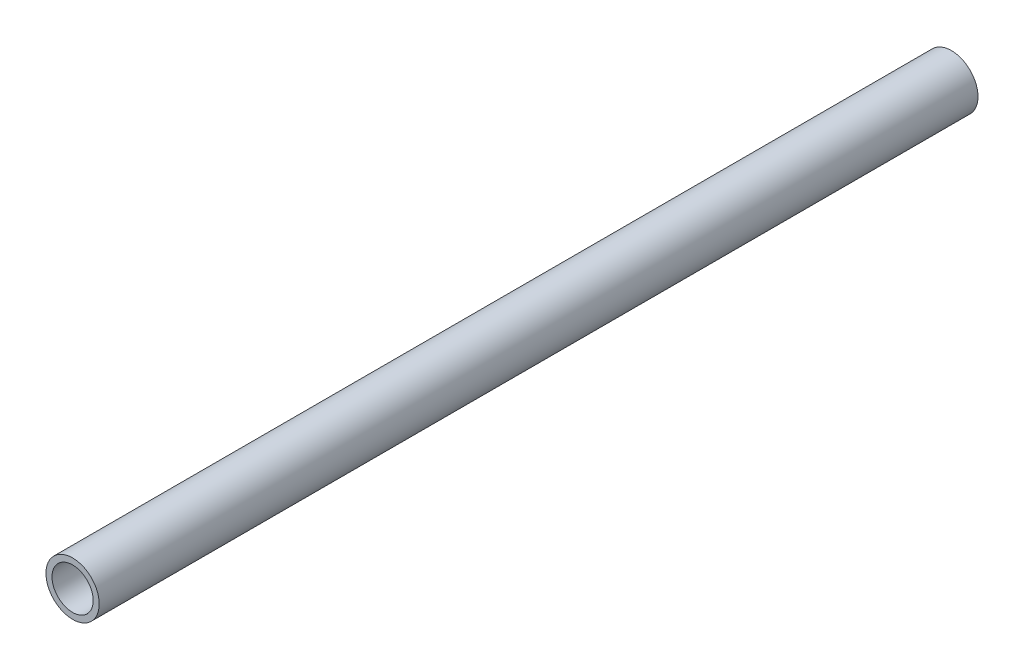
SolidWorks part; units mm, degrees
ref_plane "Front Plane" through (0, 0, 0) normal (0, 0, 1) x (1, 0, 0)
ref_plane "Top Plane" through (0, 0, 0) normal (0, 1, 0) x (1, 0, 0)
ref_plane "Right Plane" through (0, 0, 0) normal (1, 0, 0) x (0, 0, -1)
sketch "Sketch1" plane through (0, 0, 0) normal (0, 0, 1) x (1, 0, 0)
  circle A0 centre (0, 0) radius 6.1595 construction
  circle A1 centre (0, 0) radius 4.7625 construction
  point P4 (4.7625, 0)
  point P5 (6.1595, 0)
  dimension "OD" = 12.319
  dimension "ID" = 9.525
  dimension "Wall Thickness" = 1.397
sketch "Sketch2" plane through (0, 0, 0) normal (1, 0, 0) x (0, 0, -1)
  line L0 (-101.6, 0) -> (101.6, 0) construction
  line L1 (-101.6, -6.1595) -> (-101.6, 6.1595) construction
  line L2 (-101.6, 6.1595) -> (101.6, 6.1595) construction
  line L3 (101.6, -6.1595) -> (101.6, 6.1595) construction
  line L5 (-101.6, -6.1595) -> (101.6, -6.1595) construction
  point P0 (-89.281, 0)
  point P3 (0, 0)
  point P7 (0, 6.1595)
  point P8 (89.281, 0)
  point P11 (-101.6, 0)
  point P13 (101.6, 0)
  dimension "Length" = 203.2
  dimension "D1" = 12.319
  dimension "D2" = 12.319
sketch "Sketch3" plane through (0, 0, 0) normal (0, 0, 1) x (1, 0, 0)
  circle A0 centre (0, 0) radius 4.7625 construction
  circle A1 centre (0, 0) radius 6.1595 construction
  circle A2 centre (0, 0) radius 4.7625
  circle A3 centre (0, 0) radius 6.1595
extrude "Boss-Extrude1" add sketch "Sketch3" along normal up to vertex (101.6 mm away) and the other way up to vertex (101.6 mm away) up to point (0, 0, 101.6) other way up to point (0, 0, -101.6)
equation "\"D1@Sketch2\"=\"OD@Sketch1\""
equation "\"D2@Sketch2\"=\"D1@Sketch2\""
